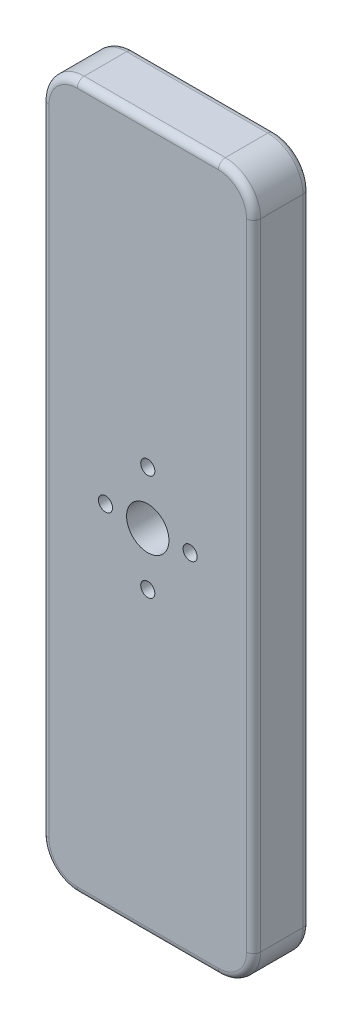
SolidWorks part; units mm, degrees
ref_plane "正面" through (0, 0, 0) normal (0, 0, 1) x (1, 0, 0)
ref_plane "平面" through (0, 0, 0) normal (0, 1, 0) x (1, 0, 0)
ref_plane "右側面" through (0, 0, 0) normal (1, 0, 0) x (0, 0, -1)
sketch "ｽｹｯﾁ1" plane through (0, 0, 0) normal (0, 0, 1) x (1, 0, 0)
  line L1 (5, 0) -> (25, 0)
  line L2 (0, 5) -> (0, 95)
  line L3 (5, 100) -> (25, 100)
  line L4 (30, 5) -> (30, 95)
  arc A0 (25, 0) -> (30, 5) centre (25, 5) ccw
  arc A1 (5, 0) -> (0, 5) centre (5, 5) cw
  arc A2 (25, 100) -> (30, 95) centre (25, 95) cw
  arc A3 (0, 95) -> (5, 100) centre (5, 95) cw
  point P9 (0, 0)
  dimension "D1" = 5
  dimension "D2" = 30
  dimension "D3" = 100
extrude "ﾎﾞｽ - 押し出し1" add sketch "ｽｹｯﾁ1" along normal blind 8
sketch "ｽｹｯﾁ2" plane through (0, 0, 0) normal (0, 0, -1) x (-1, 0, 0)
  line L0 (-25, 100) -> (-5, 100) construction
  line L2 (-30, 5) -> (-30, 95) construction
  circle A0 centre (-15, 88) radius 3
  dimension "D3" = 6
  dimension "D1" = 12
  dimension "D2" = 15
extrude "ｶｯﾄ - 押し出し1" cut sketch "ｽｹｯﾁ2" against normal blind 3 contours A0
sketch "ｽｹｯﾁ4" plane through (0, 0, 0) normal (0, 0, -1) x (-1, 0, 0)
  line L0 (-15, 95) -> (-15, 93) construction
  line L1 (-14.25, 95) -> (-14.25, 93)
  line L2 (-15.75, 95) -> (-15.75, 93)
  line L3 (-30, 5) -> (-30, 95) construction
  line L4 (-25, 100) -> (-5, 100) construction
  arc A0 (-14.25, 95) -> (-15.75, 95) centre (-15, 95) ccw
  arc A1 (-15.75, 93) -> (-14.25, 93) centre (-15, 93) ccw
  point P2 (-15, 94)
  dimension "D1" = 15
  dimension "D2" = 6
  dimension "D3" = 1.5
  dimension "D4" = 2
extrude "ｶｯﾄ - 押し出し2" cut sketch "ｽｹｯﾁ4" against normal blind 3 contours L2 A1 L1 A0
pattern_circular "円形ﾊﾟﾀｰﾝ1" count 8 over 360 about axis through (15, 88, 0) along (0, 0, 1) of "ｶｯﾄ - 押し出し2"
sketch "ｽｹｯﾁ6" plane through (0, 0, 0) normal (0, 0, -1) x (-1, 0, 0)
  line L0 (-9, 11) -> (-9.0212, 11) construction
  line L3 (-30, 5) -> (-30, 95) construction
  line L6 (-9, 13.499) -> (-21, 13.5)
  line L7 (0, 95) -> (0, 5) construction
  line L8 (-5, 0) -> (-25, 0) construction
  arc A4 (-9, 8.501) -> (-9, 13.499) centre (-9, 11) ccw
  arc A5 (-21, 13.5) -> (-21, 8.5) centre (-21, 11) ccw
  arc A6 (-17.4, 6.255) -> (-9, 8.501) centre (-13.5, 8.5) ccw
  arc A7 (-21, 8.5) -> (-17.4, 6.255) centre (-18.5, 8.5) ccw
  point P2 (-15, 11)
  dimension "D3" = 2.5
  dimension "D4" = 9
  dimension "D5" = 5
  dimension "D6" = 12
  dimension "D11" = 2.5
  dimension "D1" = 15
  dimension "D2" = 11
  dimension "D7" = 9
  dimension "D8" = 9
  dimension "D9" = 12
  dimension "D10" = 4.5
extrude "ｶｯﾄ - 押し出し3" cut sketch "ｽｹｯﾁ6" against normal blind 3
sketch "ｽｹｯﾁ12" plane through (0, 0, 0) normal (0, 0, -1) x (-1, 0, 0)
  line L0 (-16.125, 17.5825) -> (-14.875, 15.4175) construction
  line L1 (-15.259, 18.0825) -> (-14.009, 15.9175)
  line L2 (-16.991, 17.0825) -> (-15.741, 14.9175)
  line L3 (0, 95) -> (0, 5) construction
  line L4 (-5, 0) -> (-25, 0) construction
  line L5 (-5, 0) -> (-25, 0) construction
  arc A0 (-15.259, 18.0825) -> (-16.991, 17.0825) centre (-16.125, 17.5825) ccw
  arc A1 (-15.741, 14.9175) -> (-14.009, 15.9175) centre (-14.875, 15.4175) ccw
  point P2 (-15.5, 16.5)
  dimension "D1" = 1
  dimension "D2" = 2.5
  dimension "D3" = 15.5
  dimension "D4" = 16.5
  dimension "D5" = 60
extrude "ｶｯﾄ - 押し出し4" cut sketch "ｽｹｯﾁ12" against normal blind 3
pattern_linear "直線ﾊﾟﾀｰﾝ2" count 2 spacing 4 along (-1, 0, 0) of "ｶｯﾄ - 押し出し4"
pattern_linear "直線ﾊﾟﾀｰﾝ4" count 2 spacing 4 along (1, 0, 0) of "ｶｯﾄ - 押し出し4"
sketch "ｽｹｯﾁ14" plane through (0, 0, 0) normal (0, 0, -1) x (-1, 0, 0)
  line L0 (-25, 100) -> (-5, 100) construction
  line L1 (-30, 5) -> (-30, 95) construction
  circle A0 centre (-15, 50) radius 9
  dimension "D3" = 18
  dimension "D1" = 50
  dimension "D2" = 15
extrude "ｶｯﾄ - 押し出し7" cut sketch "ｽｹｯﾁ14" against normal blind 2
sketch "ｽｹｯﾁ15" plane through (0, 0, 2) normal (0, 0, -1) x (-1, 0, 0)
  circle A0 centre (-15, 50) radius 3
  circle A1 centre (-15, 50) radius 9 construction
  dimension "D1" = 6
extrude "ｶｯﾄ - 押し出し8" cut sketch "ｽｹｯﾁ15" against normal through all
sketch "Sketch1" plane through (0, 0, 2) normal (0, 0, -1) x (-1, 0, 0)
  line L0 (-30, 5) -> (-30, 95) construction
  circle A0 centre (-15, 57.5) radius 1
  circle A2 centre (-15, 50) radius 3 construction
  dimension "D3" = 2
  dimension "D2" = 7.5
  dimension "D1" = 15
extrude "Cut-Extrude1" cut sketch "Sketch1" against normal through all
pattern_circular "CirPattern1" count 2 over 360 about axis through (15, 50, 0) along (0, 0, 1) of "Cut-Extrude1"
sketch "Sketch2" plane through (0, 0, 2) normal (0, 0, -1) x (-1, 0, 0)
  line L0 (-5, 0) -> (-25, 0) construction
  circle A0 centre (-21, 50) radius 1
  circle A1 centre (-15, 50) radius 3 construction
  dimension "D2" = 6
  dimension "D3" = 2
  dimension "D1" = 50
extrude "Cut-Extrude2" cut sketch "Sketch2" against normal through all
pattern_circular "CirPattern2" count 2 over 360 about axis through (15, 50, 0) along (0, 0, 1) of "Cut-Extrude2"
sketch "Sketch3" plane through (0, 0, 8) normal (0, 0, 1) x (1, 0, 0)
  circle A0 centre (15, 57.5) radius 0.9
  dimension "D1" = 1.8
sketch "Sketch4" plane through (0, 0, 8) normal (0, 0, 1) x (1, 0, 0)
  circle A0 centre (9, 50) radius 0.9
  dimension "D1" = 1.8
fillet "Fillet1" radius 1 8 edges at (1.4645, 98.5355, 8) (15, 100, 8) (28.5355, 98.5355, 8) (30, 50, 8) (28.5355, 1.4645, 8) (15, 0, 8) (1.4645, 1.4645, 8) (0, 50, 8)
fillet "Fillet2" radius 1 8 edges at (28.5355, 1.4645, 0) (15, 0, 0) (1.4645, 1.4645, 0) (0, 50, 0) (1.4645, 98.5355, 0) (15, 100, 0) (28.5355, 98.5355, 0) (30, 50, 0)
extrude "Cut-Extrude3" [suppressed] cut sketch "Sketch3" against normal blind 1
extrude "Cut-Extrude4" [suppressed] cut sketch "Sketch4" against normal blind 1
pattern_circular "CirPattern3" [suppressed] count 2 over 360
pattern_circular "CirPattern4" [suppressed] count 2 over 360
